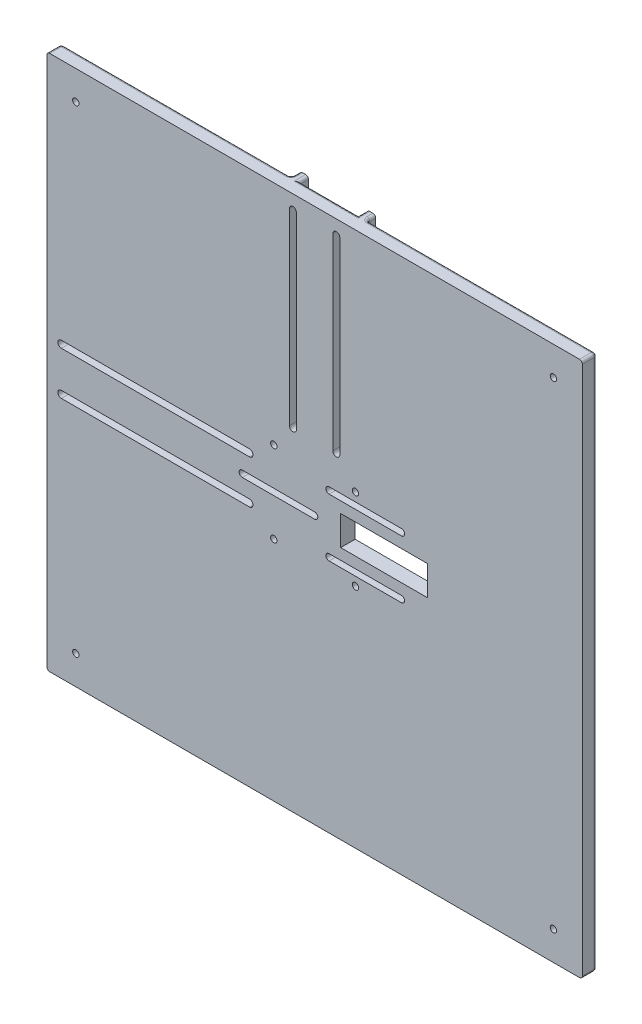
SolidWorks part; units mm, degrees
ref_plane "Plan de face" through (0, 0, 0) normal (0, 0, 1) x (1, 0, 0)
ref_plane "Plan de dessus" through (0, 0, 0) normal (0, 1, 0) x (1, 0, 0)
ref_plane "Plan de droite" through (0, 0, 0) normal (1, 0, 0) x (0, 0, -1)
sketch "Esquisse1" plane through (0, 0, 0) normal (0, 0, 1) x (1, 0, 0)
  line L1 (-92.5, 92.5) -> (92.5, 92.5)
  line L2 (-92.5, 92.5) -> (-92.5, -92.5)
  line L3 (-92.5, -92.5) -> (92.5, -92.5)
  line L4 (92.5, 92.5) -> (92.5, -92.5)
  dimension "D1" = 185
  dimension "D2" = 185
  dimension "D3" = 92.5
  dimension "D4" = 92.5
extrude "Boss.-Extru.1" add sketch "Esquisse1" along normal blind 5
sketch "Esquisse2" plane through (0, 0, 0) normal (0, 0, -1) x (-1, 0, 0)
  line L1 (22.5, 10.1) -> (92.5, 10.1)
  line L4 (92.5, 10.1) -> (92.5, 13.1)
  line L5 (92.5, -13.1) -> (22.5, -13.1)
  line L6 (92.5, -13.1) -> (92.5, -10.1)
  line L7 (92.5, -10.1) -> (22.5, -10.1)
  line L19 (92.5, 92.5) -> (92.5, -92.5) construction
  line L24 (13.1, 22.5) -> (13.1, 92.5)
  line L25 (-92.5, 92.5) -> (92.5, 92.5) construction
  line L26 (10.1, 22.5) -> (10.1, 92.5)
  line L28 (-13.1, 92.5) -> (-10.1, 92.5)
  line L29 (10.1, 92.5) -> (13.1, 92.5)
  line L31 (-10.1, 92.5) -> (-10.1, 22.5)
  line L32 (-13.1, 92.5) -> (-13.1, 22.5)
  line L33 (-10.1, 22.5) -> (-13.1, 22.5)
  line L35 (22.5, -10.1) -> (22.5, -13.1)
  line L36 (92.5, 13.1) -> (22.5, 13.1)
  line L37 (22.5, 13.1) -> (22.5, 10.1)
  line L38 (13.1, 22.5) -> (10.1, 22.5)
  dimension "D1" = 20.2
  dimension "D2" = 3
  dimension "D3" = 3
  dimension "D4" = 10.1
  dimension "D5" = 3
  dimension "D6" = 3
  dimension "D7" = 20.2
  dimension "D8" = 10.1
  dimension "D9" = 70
  dimension "D10" = 70
extrude "Boss.-Extru.2" add sketch "Esquisse2" along normal blind 3
fillet "Congé1" radius 1 32 edges at (-13.1, 57.5, 0) (-57.5, -13.1, 0) (-13.1, 92.5, -1.5) (-92.5, -13.1, -1.5) (92.5, -92.5, 2.5) (92.5, 92.5, 2.5) (92.5, 0, 0) (0, 92.5, 0) (-92.5, 0, 0) (-52.8, 92.5, 0) (-92.5, 52.8, 0) (-92.5, 92.5, 2.5) (52.8, 92.5, 0) (0, -92.5, 0) (-92.5, -52.8, 0) (-92.5, -92.5, 2.5) (-10.1, 92.5, -1.5) (-92.5, 10.1, -1.5) (-92.5, -10.1, -1.5) (13.1, 92.5, -1.5) (10.1, 92.5, -1.5) (13.1, 57.5, 0) (-92.5, 13.1, -1.5) (-57.5, 13.1, 0) (-22.5, -11.6, 0) (11.6, 22.5, 0) (-11.6, 22.5, 0) (-22.5, 11.6, 0) (-22.5, -13.1, -1.5) (13.1, 22.5, -1.5) (-13.1, 22.5, -1.5) (-22.5, 13.1, -1.5)
sketch "Esquisse4" plane through (0, 0, 0) normal (0, 0, -1) x (-1, 0, 0)
  line L4 (-92.5, -91.5) -> (-92.5, 91.5) construction
  line L5 (91.5, -92.5) -> (-91.5, -92.5) construction
  line L6 (-91.5, 92.5) -> (-14.1, 92.5) construction
  line L7 (92.5, -14.1) -> (92.5, -91.5) construction
  circle A0 centre (-14.1, 14.1) radius 1.1
  circle A1 centre (14.1, 14.1) radius 1.1
  circle A2 centre (14.1, -14.1) radius 1.1
  circle A3 centre (-14.1, -14.1) radius 1.1
  circle A4 centre (-82.5, -82.5) radius 1.1
  circle A5 centre (-82.5, 82.5) radius 1.1
  circle A6 centre (82.5, -82.5) radius 1.1
  circle A7 centre (82.5, 82.5) radius 1.1
  dimension "D1" = 2.2
  dimension "D4" = 4
  dimension "D5" = 4
  dimension "D6" = 10
  dimension "D7" = 10
  dimension "D8" = 10
  dimension "D9" = 10
  dimension "D10" = 4
  dimension "D11" = 4
extrude "Enlèv. mat.-Extru.1" cut sketch "Esquisse4" against normal up to next
sketch "Esquisse5" plane through (0, 0, 0) normal (0, 0, -1) x (-1, 0, 0)
  line L0 (-7.5, 87.5) -> (-7.5, 22.5) construction
  line L1 (-6.3, 87.5) -> (-6.3, 22.5)
  line L2 (-8.7, 87.5) -> (-8.7, 22.5)
  line L3 (7.5, 87.5) -> (7.5, 22.5) construction
  line L4 (8.7, 87.5) -> (8.7, 22.5)
  line L5 (6.3, 87.5) -> (6.3, 22.5)
  line L9 (10.1, 91.5) -> (10.1, 21.5) construction
  line L10 (-10.1, 92.5) -> (10.1, 92.5) construction
  line L11 (-10.1, 21.5) -> (-10.1, 91.5) construction
  line L12 (-91.5, 92.5) -> (-14.1, 92.5) construction
  arc A0 (-6.3, 87.5) -> (-8.7, 87.5) centre (-7.5, 87.5) ccw
  arc A1 (-8.7, 22.5) -> (-6.3, 22.5) centre (-7.5, 22.5) ccw
  arc A2 (8.7, 87.5) -> (6.3, 87.5) centre (7.5, 87.5) ccw
  arc A3 (6.3, 22.5) -> (8.7, 22.5) centre (7.5, 22.5) ccw
  point P2 (-7.5, 55)
  point P7 (7.5, 55)
  dimension "D1" = 1.2
  dimension "D2" = 1.2
  dimension "D3" = 2.6
  dimension "D4" = 5
  dimension "D6" = 2.6
  dimension "D7" = 70
extrude "Enlèv. mat.-Extru.2" cut sketch "Esquisse5" against normal through all
sketch "Esquisse6" plane through (0, 0, 0) normal (0, 0, -1) x (-1, 0, 0)
  line L0 (87.5, -7.5) -> (22.5, -7.5) construction
  line L1 (87.5, -8.7) -> (22.5, -8.7)
  line L2 (87.5, -6.3) -> (22.5, -6.3)
  line L3 (22.5, 7.5) -> (87.5, 7.5) construction
  line L4 (22.5, 8.7) -> (87.5, 8.7)
  line L5 (22.5, 6.3) -> (87.5, 6.3)
  line L6 (91.5, -10.1) -> (21.5, -10.1) construction
  line L7 (21.5, 10.1) -> (91.5, 10.1) construction
  line L8 (92.5, 10.1) -> (92.5, -10.1) construction
  arc A0 (87.5, -8.7) -> (87.5, -6.3) centre (87.5, -7.5) ccw
  arc A1 (22.5, -6.3) -> (22.5, -8.7) centre (22.5, -7.5) ccw
  arc A2 (22.5, 8.7) -> (22.5, 6.3) centre (22.5, 7.5) ccw
  arc A3 (87.5, 6.3) -> (87.5, 8.7) centre (87.5, 7.5) ccw
  point P2 (55, -7.5)
  point P7 (55, 7.5)
  dimension "D1" = 1.2
  dimension "D2" = 1.2
  dimension "D3" = 2.6
  dimension "D4" = 2.6
  dimension "D5" = 5
  dimension "D7" = 70
extrude "Enlèv. mat.-Extru.3" cut sketch "Esquisse6" against normal up to next
sketch "Esquisse9" plane through (0, 0, 5) normal (0, 0, 1) x (1, 0, 0)
  line L0 (-25, 0) -> (0, 0) construction
  line L1 (-25, 1.1) -> (0, 1.1)
  line L2 (-25, -1.1) -> (0, -1.1)
  line L3 (5, 10) -> (30, 10) construction
  line L4 (5, 11.1) -> (30, 11.1)
  line L5 (5, 8.9) -> (30, 8.9)
  line L6 (5, -10) -> (30, -10) construction
  line L7 (5, -8.9) -> (30, -8.9)
  line L8 (5, -11.1) -> (30, -11.1)
  arc A0 (-25, 1.1) -> (-25, -1.1) centre (-25, 0) ccw
  arc A1 (0, -1.1) -> (0, 1.1) centre (0, 0) ccw
  arc A2 (5, 11.1) -> (5, 8.9) centre (5, 10) ccw
  arc A3 (30, 8.9) -> (30, 11.1) centre (30, 10) ccw
  arc A4 (5, -8.9) -> (5, -11.1) centre (5, -10) ccw
  arc A5 (30, -11.1) -> (30, -8.9) centre (30, -10) ccw
  point P3 (-12.5, 0)
  point P8 (17.5, 10)
  point P15 (17.5, -10)
  point P22 (0, 0)
  dimension "D4" = 25
  dimension "D5" = 30
  dimension "D1" = 2.2
  dimension "D2" = 2.2
  dimension "D3" = 2.2
  dimension "D6" = 25
  dimension "D7" = 10
  dimension "D8" = 10
  dimension "D9" = 25
extrude "Enlèv. mat.-Extru.5" cut sketch "Esquisse9" against normal up to next
sketch "Esquisse11" plane through (0, 0, 0) normal (0, 0, -1) x (-1, 0, 0)
  line L1 (-9, 5.1) -> (-39, 5.1)
  line L2 (-9, 5.1) -> (-9, -5.1)
  line L3 (-9, -5.1) -> (-39, -5.1)
  line L4 (-39, 5.1) -> (-39, -5.1)
  dimension "D1" = 9
  dimension "D2" = 10.2
  dimension "D3" = 5.1
  dimension "D4" = 30
extrude "Enlèv. mat.-Extru.7" cut sketch "Esquisse11" against normal up to next
sketch "Esquisse12" plane through (0, 0, 0) normal (0, 0, -1) x (-1, 0, 0)
  line L1 (-33, 12.1) -> (-2, 12.1)
  line L2 (-33, 12.1) -> (-33, 7.8)
  line L3 (-33, 7.8) -> (-2, 7.8)
  line L4 (-2, 12.1) -> (-2, 7.8)
  line L5 (-33, -7.9) -> (-2, -7.9)
  line L6 (-33, -7.9) -> (-33, -12.2)
  line L7 (-33, -12.2) -> (-2, -12.2)
  line L8 (-2, -7.9) -> (-2, -12.2)
  line L9 (-3, 2.1) -> (28, 2.1)
  line L10 (-3, 2.1) -> (-3, -2.2)
  line L11 (-3, -2.2) -> (28, -2.2)
  line L12 (28, 2.1) -> (28, -2.2)
  arc A0 (-30, 11.1) -> (-30, 8.9) centre (-30, 10) ccw construction
  arc A1 (-30, -8.9) -> (-30, -11.1) centre (-30, -10) ccw construction
  arc A2 (-5, -11.1) -> (-5, -8.9) centre (-5, -10) ccw construction
  arc A3 (0, 1.1) -> (0, -1.1) centre (0, 0) ccw construction
  arc A4 (25, -1.1) -> (25, 1.1) centre (25, 0) ccw construction
  arc A5 (-5, 8.9) -> (-5, 11.1) centre (-5, 10) ccw construction
  point P15 (-31.1, 10)
  point P20 (-31.1, -10)
  dimension "D7" = 3
  dimension "D8" = 3
  dimension "D9" = 3
  dimension "D10" = 3
  dimension "D11" = 3
  dimension "D12" = 3
  dimension "D1" = 2.1
  dimension "D2" = 4.3
  dimension "D3" = 2.1
  dimension "D4" = 4.3
  dimension "D5" = 2.1
  dimension "D6" = 4.3
extrude "Enlèv. mat.-Extru.9" cut sketch "Esquisse12" against normal blind 2
fillet "Congé2" radius 0.5 11 edges at (33, -12.2, 1) (33, -7.9, 1) (2, -7.9, 1) (2, -12.2, 1) (-28, -2.2, 1) (-28, 2.1, 1) (3, -2.2, 1) (3, 2.1, 1) (2, 12.1, 1) (33, 7.8, 1) (33, 12.1, 1)
sketch "Esquisse13" plane through (0, 0, 0) normal (0, 0, -1) x (-1, 0, 0)
  line L0 (-14.1, 91.5) -> (-91.5, 91.5) construction
  line L1 (-80, -82.5) -> (-81.25, -80.3349)
  line L2 (-81.25, -80.3349) -> (-83.75, -80.3349)
  line L3 (-83.75, -80.3349) -> (-85, -82.5)
  line L4 (-85, -82.5) -> (-83.75, -84.6651)
  line L5 (-83.75, -84.6651) -> (-81.25, -84.6651)
  line L6 (-81.25, -84.6651) -> (-80, -82.5)
  line L7 (83.75, -84.6651) -> (85, -82.5)
  line L8 (85, -82.5) -> (83.75, -80.3349)
  line L9 (83.75, -80.3349) -> (81.25, -80.3349)
  line L10 (81.25, -80.3349) -> (80, -82.5)
  line L11 (80, -82.5) -> (81.25, -84.6651)
  line L12 (81.25, -84.6651) -> (83.75, -84.6651)
  line L13 (85, 82.5) -> (83.75, 84.6651)
  line L14 (83.75, 84.6651) -> (81.25, 84.6651)
  line L15 (81.25, 84.6651) -> (80, 82.5)
  line L16 (80, 82.5) -> (81.25, 80.3349)
  line L17 (81.25, 80.3349) -> (83.75, 80.3349)
  line L18 (83.75, 80.3349) -> (85, 82.5)
  line L19 (-80, 82.5) -> (-81.25, 84.6651)
  line L20 (-81.25, 84.6651) -> (-83.75, 84.6651)
  line L21 (-83.75, 84.6651) -> (-85, 82.5)
  line L22 (-85, 82.5) -> (-83.75, 80.3349)
  line L23 (-83.75, 80.3349) -> (-81.25, 80.3349)
  line L24 (-81.25, 80.3349) -> (-80, 82.5)
  line L25 (91.5, 91.5) -> (14.1, 91.5) construction
  line L26 (-91.5, -91.5) -> (91.5, -91.5) construction
  circle A0 centre (-82.5, -82.5) radius 2.1651 construction
  circle A1 centre (82.5, -82.5) radius 2.1651 construction
  circle A2 centre (82.5, 82.5) radius 2.1651 construction
  circle A3 centre (-82.5, 82.5) radius 2.1651 construction
  dimension "D1" = 2.5
  dimension "D2" = 2.5
  dimension "D3" = 2.5
  dimension "D4" = 2.5
extrude "Enlèv. mat.-Extru.10" cut sketch "Esquisse13" against normal blind 3
